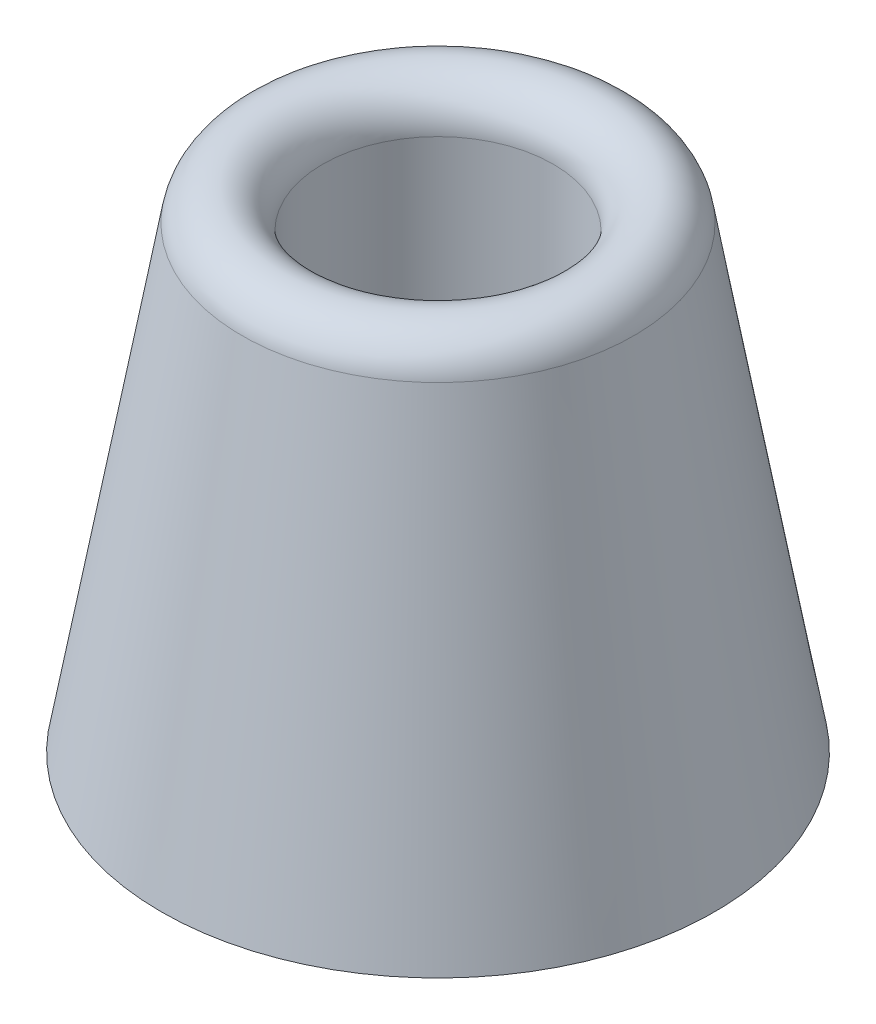
SolidWorks part; units mm, degrees
ref_plane "Front Plane" through (0, 0, 0) normal (0, 0, 1) x (1, 0, 0)
ref_plane "Top Plane" through (0, 0, 0) normal (0, 1, 0) x (1, 0, 0)
ref_plane "Right Plane" through (0, 0, 0) normal (1, 0, 0) x (0, 0, -1)
sketch "Sketch1" plane through (0, 0, 0) normal (0, 0, 1) x (1, 0, 0)
  line L0 (-14.2875, 0) -> (14.2875, 0) construction
  line L1 (0, 0) -> (0, 25.4) construction
  line L2 (-3.175, 12.7) -> (3.175, 12.7) construction
  line L3 (14.2875, 0) -> (14.2875, 13.8906) construction
  line L4 (-5.9531, 25.4) -> (5.9531, 25.4) construction
  point P5 (0, 12.7)
sketch "Sketch2" plane through (0, 0, 0) normal (0, 0, 1) x (1, 0, 0)
  line L0 (14.2875, 0) -> (3.175, 0)
  line L1 (-14.2875, 0) -> (14.2875, 0) construction
  line L2 (3.175, 0) -> (0, 0) construction
  line L3 (3.175, 0) -> (3.175, 13.8906)
  line L4 (3.175, 13.8906) -> (5.9531, 13.8906)
  line L5 (14.2875, 0) -> (10.1143, 23.6676)
  line L6 (5.9531, 13.8906) -> (5.9531, 23.3035)
  line L7 (-5.9531, 25.4) -> (5.9531, 25.4) construction
  line L8 (14.2875, 0) -> (14.2875, 13.8906) construction
  line L9 (0, 0) -> (0, 25.4) construction
  arc A0 (5.9531, 23.3035) -> (10.1143, 23.6676) centre (8.0496, 23.3035) cw
  dimension "D1" = 3.175
  dimension "D2" = 13.8906
  dimension "D3" = 10
revolve "Revolve1" add sketch "Sketch2" angle 360 about L9
equation "\"D1@Sketch2\"=\"MOUNTING HOLE DIA@Sketch1\"/2"
equation "\"D2@Sketch2\"=\"MOUNTING SURFACE HEIGHT@Sketch1\""
